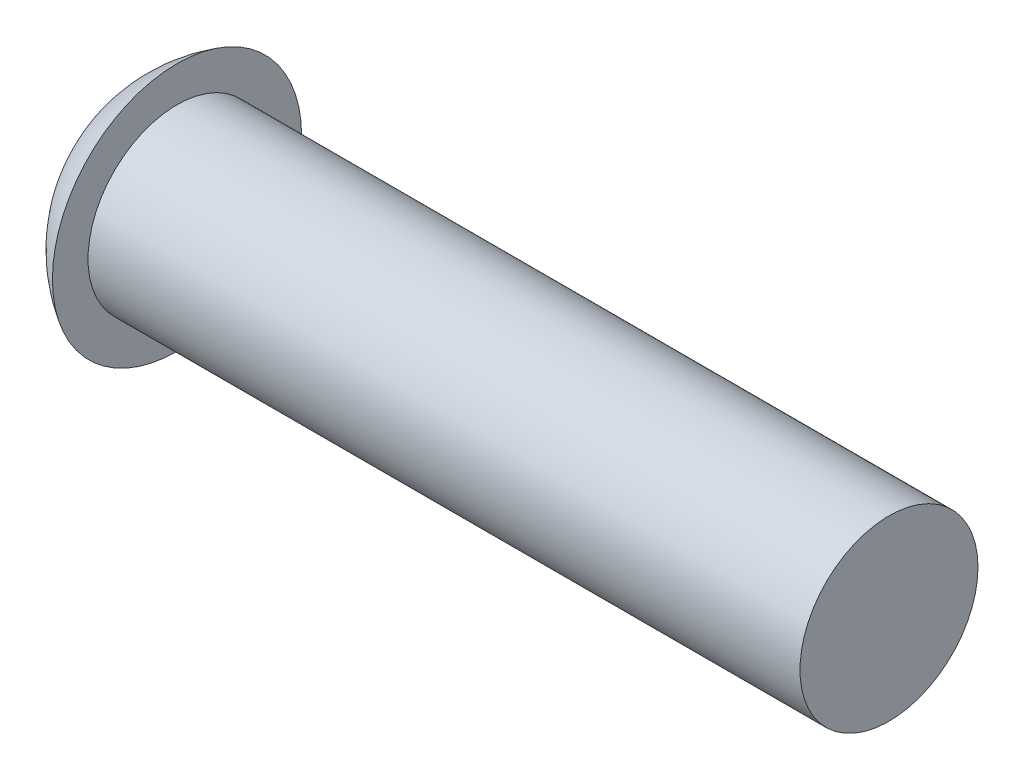
SolidWorks part; units mm, degrees
ref_plane "Front Plane" through (0, 0, 0) normal (0, 0, 1) x (1, 0, 0)
ref_plane "Top Plane" through (0, 0, 0) normal (0, 1, 0) x (1, 0, 0)
ref_plane "Right Plane" through (0, 0, 0) normal (1, 0, 0) x (0, 0, -1)
sketch "Sketch2" plane through (0, 0, 0) normal (0, 1, 0) x (1, 0, 0)
  line L0 (0, 0) -> (66.9668, 0) construction
  line L1 (110, 0) -> (110, 12.5)
  line L2 (110, 12.5) -> (10, 12.5)
  line L3 (10, 12.5) -> (10, 17.5)
  line L4 (110, 0) -> (110, -12.5) construction
  line L5 (110, 0) -> (0, 0)
  arc A0 (10, 17.5) -> (0, 0) centre (20.3125, 0) ccw
  point P10 (0, 0)
  point P11 (0, 0)
  dimension "D1" = 100
  dimension "D2" = 5
  dimension "D3" = 10
  dimension "D4" = 25
revolve "Revolve1" add sketch "Sketch2" angle 360 about L5
